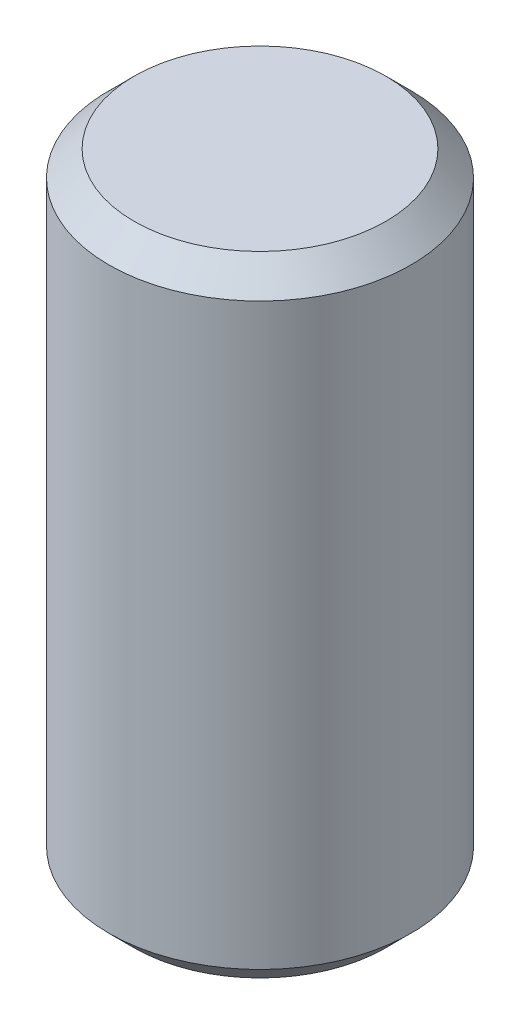
SolidWorks part; units mm, degrees
ref_plane "Front" through (0, 0, 0) normal (0, 0, 1) x (1, 0, 0)
ref_plane "Top" through (0, 0, 0) normal (0, 1, 0) x (1, 0, 0)
ref_plane "Right" through (0, 0, 0) normal (1, 0, 0) x (0, 0, -1)
sketch "Sketch1" plane through (0, 0, 0) normal (0, 0, 1) x (1, 0, 0)
  line L0 (0, 6.0802) -> (0, -6.0802) construction
  line L1 (0, -6.35) -> (3.048, -6.35)
  line L2 (3.048, -6.35) -> (3.048, 6.35)
  line L3 (3.048, 6.35) -> (0, 6.35)
  line L4 (0, 6.35) -> (0, -6.35)
  point P6 (0, 0)
  dimension "D1" = 6.096
  dimension "D2" = 12.7
revolve "Revolve1" add sketch "Sketch1" angle 360 about L0
chamfer "Chamfer1" distance 0.508 angle 45 2 edges at (0, -6.35, 3.048) (0, 6.35, 3.048)
